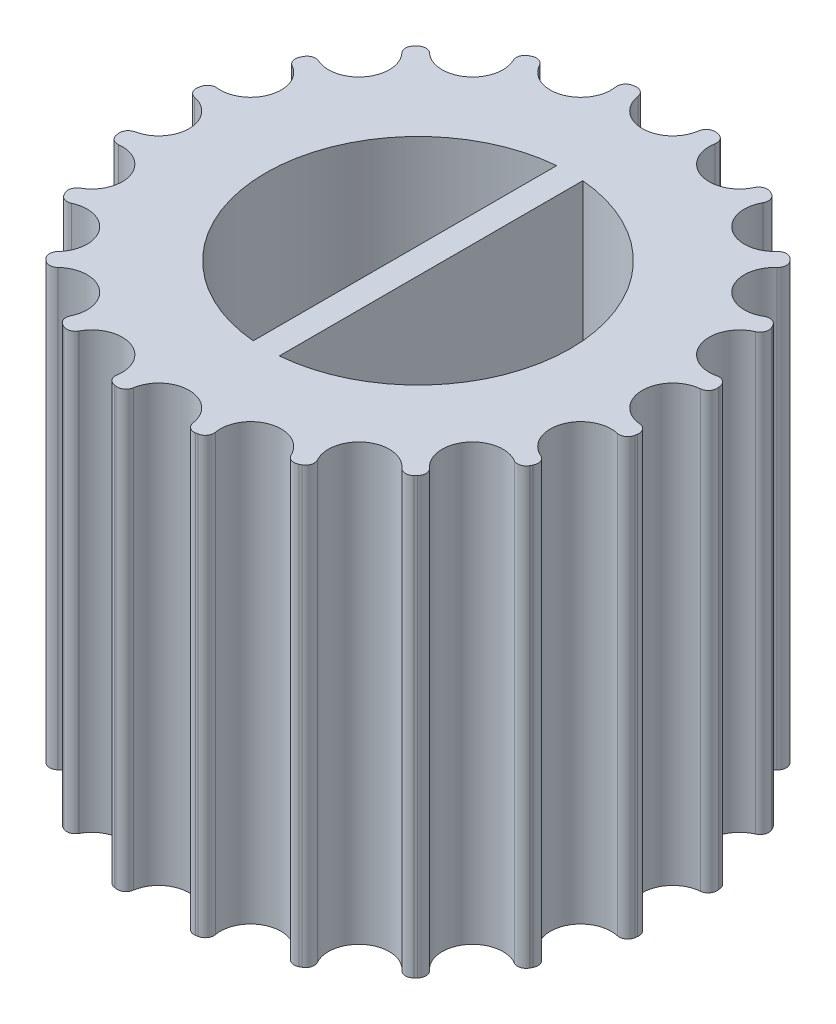
SolidWorks part; units mm, degrees
ref_plane "Front Plane" through (0, 0, 0) normal (0, 0, 1) x (1, 0, 0)
ref_plane "Top Plane" through (0, 0, 0) normal (0, 1, 0) x (1, 0, 0)
ref_plane "Right Plane" through (0, 0, 0) normal (1, 0, 0) x (0, 0, -1)
sketch "Sketch1" plane through (0, 0, 0) normal (0, 1, 0) x (1, 0, 0)
  line L804 (-1.8913, 5.8208) -> (-3.5975, 4.9515)
  line L805 (6.1204, 0) -> (5.8208, 1.8913)
  line L806 (5.8208, 1.8913) -> (4.9515, 3.5975)
  line L807 (4.9515, 3.5975) -> (3.5975, 4.9515)
  line L808 (3.5975, 4.9515) -> (1.8913, 5.8208)
  line L809 (1.8913, 5.8208) -> (0, 6.1204)
  line L810 (0, 6.1204) -> (-1.8913, 5.8208)
  line L811 (-3.5975, 4.9515) -> (-4.9515, 3.5975)
  line L812 (-4.9515, 3.5975) -> (-5.8208, 1.8913)
  line L813 (-5.8208, 1.8913) -> (-6.1204, 0)
  line L814 (-6.1204, 0) -> (-5.8208, -1.8913)
  line L815 (-5.8208, -1.8913) -> (-4.9515, -3.5975)
  line L816 (-4.9515, -3.5975) -> (-3.5975, -4.9515)
  line L817 (-3.5975, -4.9515) -> (-1.8913, -5.8208)
  line L818 (-1.8913, -5.8208) -> (0, -6.1204)
  line L819 (0, -6.1204) -> (1.8913, -5.8208)
  line L820 (1.8913, -5.8208) -> (3.5975, -4.9515)
  line L821 (3.5975, -4.9515) -> (4.9515, -3.5975)
  line L822 (4.9515, -3.5975) -> (5.8208, -1.8913)
  line L823 (5.8208, -1.8913) -> (6.1204, 0)
  line L824 (-6.1204, 0) -> (6.1204, 0) construction
  circle A2 centre (0, 0) radius 6.045 construction
  dimension "D4" = 12.09
extrude "Boss-Extrude1" add sketch "Sketch1" along normal blind 10 contours L822 L823 L805 L806 L807 L808 L809 L810 L804 L811 L812 L813 L814 L815 L816 L817 L818 L819 L820 L821
sketch "Sketch2" plane through (0, 10, 0) normal (0, 1, 0) x (1, 0, 0)
  line L0 (0, 0) -> (6.1204, 0) construction
  circle A0 centre (5.855, 0) radius 0.7
  dimension "D1" = 1.4
  dimension "D2" = 5.855
extrude "Cut-Extrude1" cut sketch "Sketch2" against normal up to next (10 mm away)
pattern_circular "CirPattern3" count 20 over 360 about axis through (-0.0525, 0, 0) along (0, 1, 0) of "Cut-Extrude1"
fillet "Fillet1" radius 0.2 40 edges at (6.0123, 5, -0.6821) (6.0123, 5, 0.6821) (5.9263, 5, -1.2254) (5.4993, 5, -2.5223) (5.2514, 5, -3.0089) (4.4386, 5, -4.1103) (4.0578, 5, -4.4911) (2.9383, 5, -5.2873) (2.4671, 5, -5.5274) (1.1504, 5, -5.9382) (0.6385, 5, -6.0192) (-0.746, 5, -6.0022) (-1.2476, 5, -5.9227) (-2.5638, 5, -5.4781) (-3.0083, 5, -5.2517) (-4.1268, 5, -4.4221) (-4.4746, 5, -4.0744) (-5.2864, 5, -2.9401) (-5.5075, 5, -2.5062) (-5.934, 5, -1.1768) (-6.0098, 5, -0.6982) (-6.0098, 5, 0.6982) (-5.934, 5, 1.1768) (-5.5075, 5, 2.5062) (-5.2864, 5, 2.9401) (-4.4746, 5, 4.0744) (-4.1268, 5, 4.4221) (-3.0083, 5, 5.2517) (-2.5638, 5, 5.4781) (-1.2476, 5, 5.9227) (-0.746, 5, 6.0022) (0.6385, 5, 6.0192) (1.1504, 5, 5.9382) (2.4671, 5, 5.5274) (2.9383, 5, 5.2873) (4.0578, 5, 4.4911) (4.4386, 5, 4.1103) (5.2514, 5, 3.0089) (5.4993, 5, 2.5223) (5.9263, 5, 1.2254)
sketch "Sketch3" plane through (0, 10, 0) normal (0, 1, 0) x (1, 0, 0)
  circle A0 centre (0, 0) radius 3.5
  dimension "D1" = 7
extrude "Cut-Extrude2" cut sketch "Sketch3" against normal up to next
ref_plane "Plane1" through (0, 5, 0) normal (0, -1, 0) x (-1, 0, 0)
sketch "Sketch4" plane through (0, 0, 0) normal (0, -1, 0) x (1, 0, 0)
  line L1 (0.3, -5.2075) -> (-0.3, -5.2075)
  line L2 (0.3, -5.2075) -> (0.3, 5.2075)
  line L3 (0.3, 5.2075) -> (-0.3, 5.2075)
  line L4 (-0.3, -5.2075) -> (-0.3, 5.2075)
  line L5 (0.3, -5.2075) -> (-0.3, 5.2075) construction
  line L6 (0.3, 5.2075) -> (-0.3, -5.2075) construction
  arc A0 (-0.7441, 5.7995) -> (0.641, 5.8122) centre (-0.0525, 5.9075) ccw construction
  point P0 (0, 0)
  dimension "D1" = 0.6
extrude "Boss-Extrude2" add sketch "Sketch4" against normal up to surface (10 mm away) up to face at (0, 10, 3.5)
